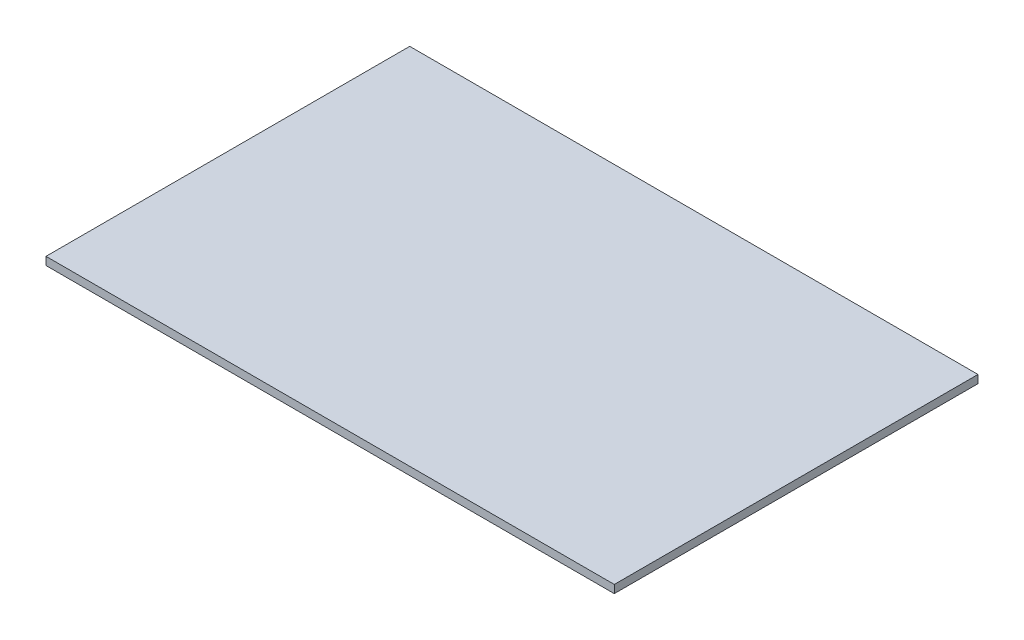
SolidWorks part; units mm, degrees
material "Pine"
ref_plane "Front Plane" through (0, 0, 0) normal (0, 0, 1) x (1, 0, 0)
ref_plane "Top Plane" through (0, 0, 0) normal (0, 1, 0) x (1, 0, 0)
ref_plane "Right Plane" through (0, 0, 0) normal (1, 0, 0) x (0, 0, -1)
sketch "Sketch1" plane through (0, 0, 0) normal (0, 1, 0) x (1, 0, 0)
  line L1 (-635, -406.4) -> (635, -406.4)
  line L2 (-635, -406.4) -> (-635, 406.4)
  line L3 (-635, 406.4) -> (635, 406.4)
  line L4 (635, -406.4) -> (635, 406.4)
  line L5 (-635, -406.4) -> (635, 406.4) construction
  line L6 (-635, 406.4) -> (635, -406.4) construction
  point P0 (0, 0)
  dimension "D1" = 812.8
  dimension "D2" = 1270
extrude "Boss-Extrude1" add sketch "Sketch1" along normal blind 17.8816
